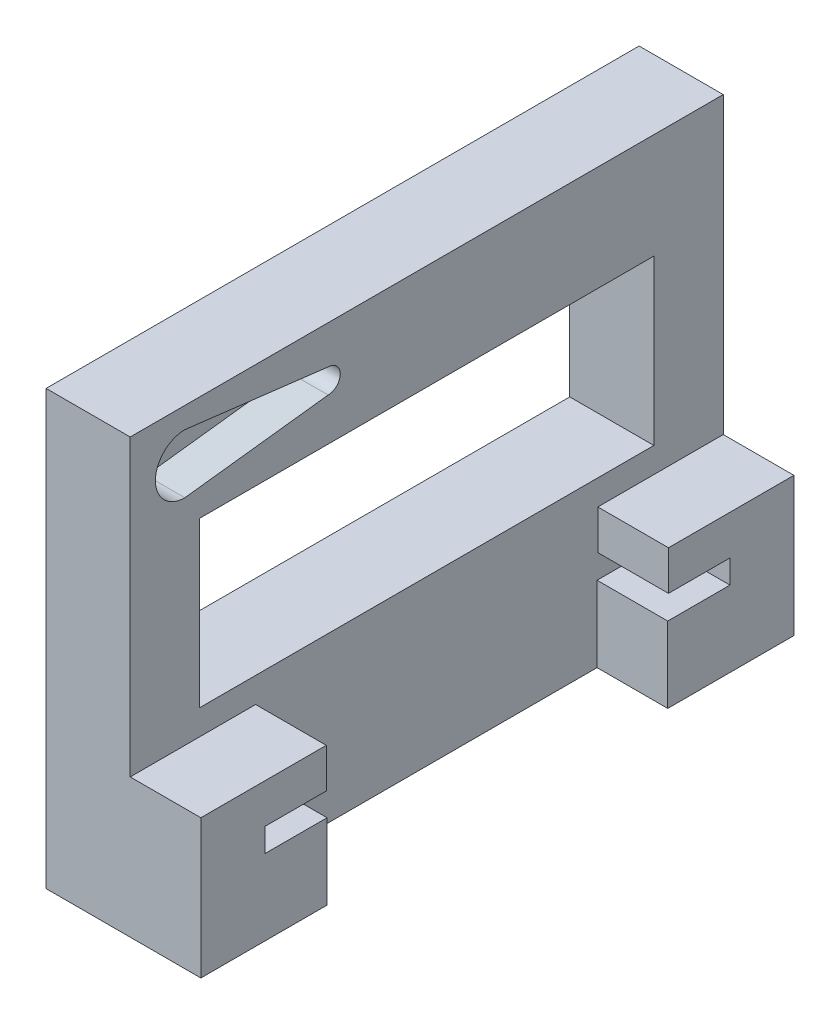
SolidWorks part; units mm, degrees
ref_plane "Front Plane" through (0, 0, 0) normal (0, 0, 1) x (1, 0, 0)
ref_plane "Top Plane" through (0, 0, 0) normal (0, 1, 0) x (1, 0, 0)
ref_plane "Right Plane" through (0, 0, 0) normal (1, 0, 0) x (0, 0, -1)
sketch "Sketch1" plane through (0, 0, 0) normal (0, 1, 0) x (1, 0, 0)
  line L1 (0, 0) -> (8.4, 0) construction
  line L2 (0, 0) -> (0, 40.5) construction
  line L3 (0, 40.5) -> (8.4, 40.5) construction
  line L4 (8.4, 0) -> (8.4, 40.5)
  line L5 (8.4, 55.5) -> (-10, 55.5)
  line L6 (8.4, 55.5) -> (8.4, -15)
  line L7 (8.4, -15) -> (-10, -15)
  line L8 (-10, 55.5) -> (-10, -15)
  dimension "D1" = 40.5
  dimension "D2" = 8.4
  dimension "D3" = 15
  dimension "D4" = 15
  dimension "D5" = 10
  dimension "D6" = 8.4
extrude "Boss-Extrude1" add sketch "Sketch1" along normal blind 9 contours L5 L8 L7 L6 L4
sketch "Sketch2" plane through (0, 9, 0) normal (0, 1, 0) x (1, 0, 0)
  line L0 (8.4, 55.5) -> (8.4, -15) construction
  line L1 (0, 0) -> (8.4, 0)
  line L2 (0, 0) -> (0, 40.5)
  line L3 (0, 40.5) -> (8.4, 40.5)
  line L4 (8.4, 0) -> (8.4, 40.5)
  dimension "D1" = 40.5
extrude "Cut-Extrude1" cut sketch "Sketch2" against normal blind 40.4
sketch "Sketch3" plane through (0, 9, 0) normal (0, 1, 0) x (1, 0, 0)
  line L1 (-10, 55.5) -> (8.4, 55.5)
  line L2 (-10, 55.5) -> (-10, -15)
  line L3 (-10, -15) -> (8.4, -15)
  line L4 (8.4, 55.5) -> (8.4, -15)
extrude "Boss-Extrude2" add sketch "Sketch3" along normal blind 42.5
sketch "Sketch4" plane through (8.4, 0, 0) normal (1, 0, 0) x (0, 0, -1)
  line L0 (40.5, 0) -> (0, 0) construction
  line L1 (-0.09, 11.8) -> (40.59, 11.8) construction
  line L2 (-0.09, 11.8) -> (-0.09, 44.4)
  line L3 (-0.09, 44.4) -> (40.59, 44.4)
  line L4 (40.59, 11.8) -> (40.59, 44.4)
  line L5 (-7.4, 11.8) -> (-0.09, 11.8)
  line L6 (40.59, 11.8) -> (47.9, 11.8)
  line L7 (-7.4, 11.8) -> (47.9, 11.8) construction
  line L12 (-7.4, 11.8) -> (-7.4, 9)
  line L13 (-7.4, 9) -> (47.9, 9)
  line L14 (47.9, 11.8) -> (47.9, 9)
  point P4 (20.25, 0)
  point P7 (20.25, 11.8)
  point P12 (20.25, 11.8)
  point P13 (20.25, 44.4)
  dimension "D1" = 40.68
  dimension "D2" = 32.6
  dimension "D3" = 55.3
  dimension "D4" = 2.8
extrude "Cut-Extrude2" cut sketch "Sketch4" against normal blind 8.4
sketch "Sketch5" plane through (8.4, 0, 0) normal (1, 0, 0) x (0, 0, -1)
  line L0 (55.5, 51.5) -> (55.5, 0) construction
  line L1 (-15, 51.5) -> (55.5, 51.5)
  line L2 (-15, 51.5) -> (-15, 16.5)
  line L3 (-15, 16.5) -> (55.5, 16.5)
  line L4 (55.5, 51.5) -> (55.5, 16.5)
  dimension "D1" = 35
extrude "Cut-Extrude3" cut sketch "Sketch5" against normal blind 8.4
sketch "Sketch7" plane through (0, 0, 0) normal (1, 0, 0) x (0, 0, -1)
  line L0 (-8.5, 49.0028) -> (8.5259, 46.9454)
  line L1 (-8.5, 41.9972) -> (8.5259, 44.0546)
  line L2 (55.5, 51.5) -> (-15, 51.5) construction
  line L3 (-15, 51.5) -> (-15, 16.5) construction
  arc A0 (-8.5, 49.0028) -> (-8.5, 41.9972) centre (-8.5, 45.5) ccw
  arc A1 (8.5259, 44.0546) -> (8.5259, 46.9454) centre (8.5259, 45.5) ccw
  dimension "D1" = 7.0056
  dimension "D2" = 2.8908
  dimension "D3" = 6
  dimension "D4" = 6.5
  dimension "D5" = 17.0259
extrude "Cut-Extrude4" cut sketch "Sketch7" against normal blind 4.6
sketch "Sketch8" plane through (0, 0, 0) normal (1, 0, 0) x (0, 0, -1)
  line L0 (55.5, 51.5) -> (-15, 51.5) construction
  line L1 (-6.75, 38.9972) -> (47.25, 38.9972)
  line L2 (-6.75, 38.9972) -> (-6.75, 19.5)
  line L3 (-6.75, 19.5) -> (47.25, 19.5)
  line L4 (47.25, 38.9972) -> (47.25, 19.5)
  line L5 (-15, 16.5) -> (-0.09, 16.5) construction
  point P6 (20.25, 51.5)
  point P7 (20.25, 38.9972)
  dimension "D1" = 3
  dimension "D2" = 3
  dimension "D3" = 54
extrude "Cut-Extrude5" cut sketch "Sketch8" against normal through all
